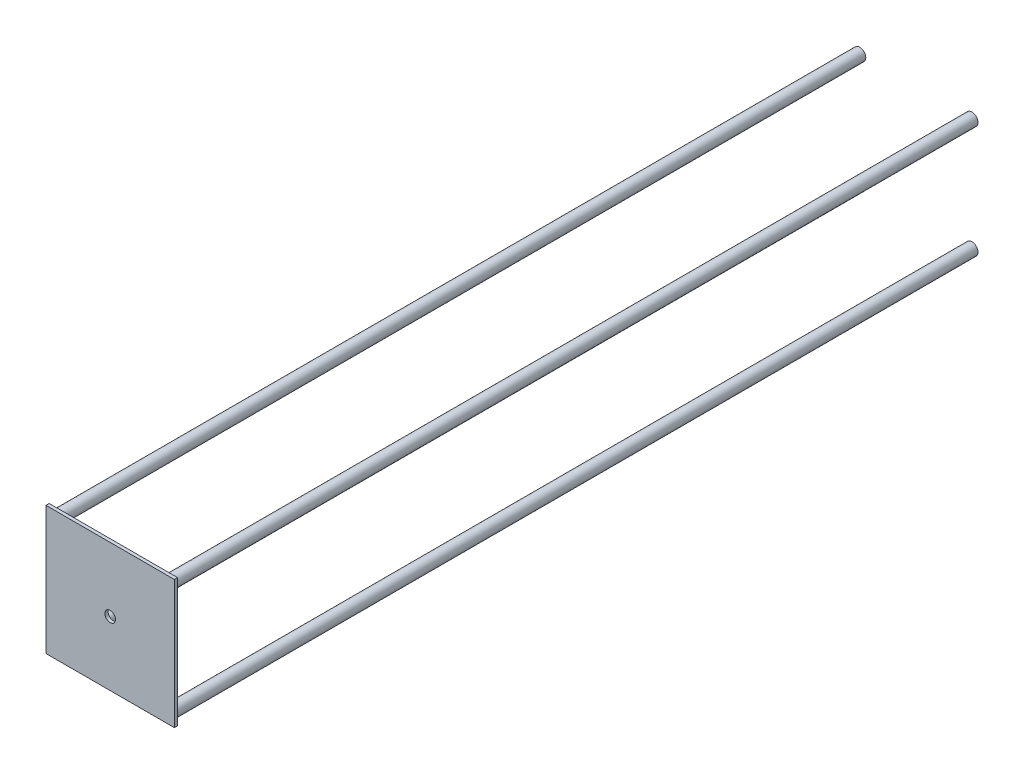
SolidWorks part; units mm, degrees
ref_plane "Front Plane" through (0, 0, 0) normal (0, 0, 1) x (1, 0, 0)
ref_plane "Top Plane" through (0, 0, 0) normal (0, 1, 0) x (1, 0, 0)
ref_plane "Right Plane" through (0, 0, 0) normal (1, 0, 0) x (0, 0, -1)
sketch "Sketch1" plane through (0, 0, 0) normal (0, 0, 1) x (1, 0, 0)
  line L1 (-50.8, -50.8) -> (50.8, -50.8)
  line L2 (-50.8, -50.8) -> (-50.8, 50.8)
  line L3 (-50.8, 50.8) -> (50.8, 50.8)
  line L4 (50.8, -50.8) -> (50.8, 50.8)
  line L5 (-50.8, -50.8) -> (50.8, 50.8) construction
  line L6 (-50.8, 50.8) -> (50.8, -50.8) construction
  point P0 (0, 0)
  dimension "D1" = 101.6
  dimension "D2" = 101.6
extrude "Boss-Extrude1" add sketch "Sketch1" along normal blind 2.54
sketch "Sketch2" plane through (0, 0, 0) normal (0, 0, -1) x (-1, 0, 0)
  line L0 (0, 50.8) -> (0, -50.8) construction
  line L1 (-50.8, 50.8) -> (50.8, 50.8) construction
  line L2 (50.8, -50.8) -> (-50.8, -50.8) construction
  line L3 (50.8, 50.8) -> (50.8, -50.8) construction
  line L4 (-50.8, -50.8) -> (-50.8, 50.8) construction
  line L5 (-50.8, 50.8) -> (50.8, 50.8) construction
  line L7 (50.8, -50.8) -> (-50.8, -50.8) construction
  circle A0 centre (-44.45, 44.45) radius 4.826
  circle A1 centre (44.3773, 44.45) radius 4.826
  circle A2 centre (44.3773, -44.45) radius 4.826
  circle A3 centre (-44.45, -44.45) radius 4.826
  point P22 (-56.2113, 43.1391)
  point P23 (0, 0)
  dimension "D1" = 9.652
  dimension "D2" = 9.652
  dimension "D3" = 9.652
  dimension "D4" = 9.652
  dimension "D5" = 6.4227
  dimension "D6" = 6.4227
  dimension "D7" = 6.35
  dimension "D8" = 6.35
  dimension "D9" = 6.35
  dimension "D10" = 6.35
  dimension "D11" = 6.35
  dimension "D12" = 6.35
extrude "Boss-Extrude2" add sketch "Sketch2" along normal blind 635 contours A2 | A3 | A0 | A1
sketch "Sketch3" plane through (0, 0, 2.54) normal (0, 0, 1) x (1, 0, 0)
  circle A0 centre (0, 0) radius 4.191
  dimension "D1" = 8.382
extrude "Cut-Extrude1" cut sketch "Sketch3" against normal blind 635
